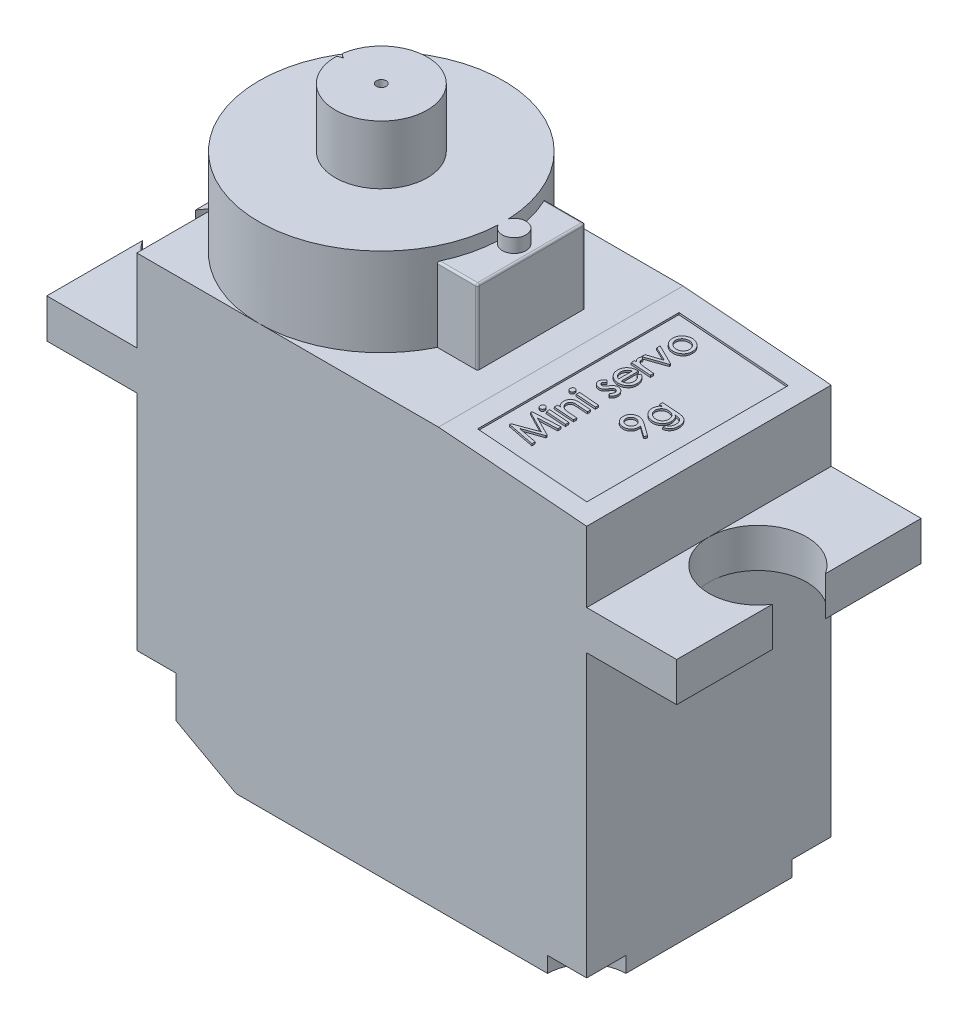
SolidWorks part; units mm, degrees
other "Camera1"
material "ABS"
ref_plane "Front Plane" through (0, 0, 0) normal (0, 0, 1) x (1, 0, 0)
ref_plane "Top Plane" through (0, 0, 0) normal (0, 1, 0) x (1, 0, 0)
ref_plane "Right Plane" through (0, 0, 0) normal (1, 0, 0) x (0, 0, -1)
sketch "Sketch1" plane through (0, 0, 0) normal (0, 1, 0) x (1, 0, 0)
  line L1 (11.5, -6.25) -> (-11.5, -6.25)
  line L2 (11.5, -6.25) -> (11.5, 6.25)
  line L3 (11.5, 6.25) -> (-11.5, 6.25)
  line L4 (-11.5, -6.25) -> (-11.5, 6.25)
  line L5 (11.5, -6.25) -> (-11.5, 6.25) construction
  line L6 (11.5, 6.25) -> (-11.5, -6.25) construction
  point P0 (0, 0)
  dimension "D1" = 12.5
  dimension "D2" = 23
extrude "Boss-Extrude1" add sketch "Sketch1" along normal blind 15.2
sketch "Sketch2" plane through (0, 15.2, 0) normal (0, 1, 0) x (1, 0, 0)
  line L1 (16.1, -6.25) -> (-16.1, -6.25)
  line L2 (16.1, -6.25) -> (16.1, 6.25)
  line L3 (16.1, 6.25) -> (-16.1, 6.25)
  line L4 (-16.1, -6.25) -> (-16.1, 6.25)
  line L5 (16.1, -6.25) -> (-16.1, 6.25) construction
  line L6 (16.1, 6.25) -> (-16.1, -6.25) construction
  point P0 (0, 0)
  dimension "D1" = 4.6
extrude "Boss-Extrude2" add sketch "Sketch2" along normal blind 2
sketch "Sketch3" plane through (0, 17.2, 0) normal (0, 1, 0) x (1, 0, 0)
  line L0 (16.1, 6.25) -> (-16.1, 6.25) construction
  line L1 (11.5, -6.25) -> (-11.5, -6.25)
  line L2 (11.5, -6.25) -> (11.5, 6.25)
  line L3 (11.5, 6.25) -> (-11.5, 6.25)
  line L4 (-11.5, -6.25) -> (-11.5, 6.25)
  line L5 (11.5, -6.25) -> (-11.5, 6.25) construction
  line L6 (11.5, 6.25) -> (-11.5, -6.25) construction
  point P0 (0, 0)
  dimension "D1" = 23
extrude "Boss-Extrude3" add sketch "Sketch3" along normal blind 4.2
sketch "Sketch4" plane through (0, 0, 6.25) normal (0, 0, 1) x (1, 0, 0)
  line L0 (11.5, 20.8) -> (3.9237, 21.4)
  line L1 (11.5, 21.4) -> (11.5, 17.2) construction
  line L2 (-11.5, 21.4) -> (11.5, 21.4) construction
  line L3 (3.9237, 21.4) -> (11.5, 21.4)
  line L4 (11.5, 21.4) -> (11.5, 20.8)
  dimension "D1" = 3.6
  dimension "D2" = 7.6
extrude "Cut-Extrude1" cut sketch "Sketch4" against normal through all
sketch "Sketch5" plane through (0, 21.4, 0) normal (0, 1, 0) x (1, 0, 0)
  line L0 (3.9237, 6.25) -> (-11.5, 6.25) construction
  line L2 (-11.5, 6.25) -> (-11.5, -6.25) construction
  line L3 (-11.5, -6.25) -> (3.9237, -6.25) construction
  circle A0 centre (-5.25, 0) radius 6.25
extrude "Boss-Extrude4" add sketch "Sketch5" along normal blind 4.5
sketch "Sketch6" plane through (0, 21.4, 0) normal (0, 1, 0) x (1, 0, 0)
  line L0 (3.9237, 6.25) -> (3.9237, -6.25) construction
  line L1 (-2.4237, -2.75) -> (2.4237, -2.75)
  line L2 (-2.4237, -2.75) -> (-2.4237, 2.75)
  line L3 (-2.4237, 2.75) -> (2.4237, 2.75)
  line L4 (2.4237, -2.75) -> (2.4237, 2.75)
  line L5 (-2.4237, -2.75) -> (2.4237, 2.75) construction
  line L6 (-2.4237, 2.75) -> (2.4237, -2.75) construction
  point P0 (0, 0)
  dimension "D1" = 1.5
  dimension "D2" = 5.5
extrude "Boss-Extrude5" add sketch "Sketch6" along normal blind 3.8
sketch "Sketch7" plane through (0, 25.2, 0) normal (0, 1, 0) x (1, 0, 0)
  circle A0 centre (1.5423, 0) radius 0.6059
extrude "Boss-Extrude7" add sketch "Sketch7" along normal up to surface (0.7 mm away) up to face at (-5.25, 25.9, 6.25)
sketch "Sketch8" plane through (0, 25.9, 0) normal (0, 1, 0) x (1, 0, 0)
  circle A0 centre (-5.25, 0) radius 2.35
  dimension "D1" = 4.7
extrude "Boss-Extrude8" add sketch "Sketch8" along normal blind 3
sketch "Sketch9" plane through (0, 0, 6.25) normal (0, 0, 1) x (1, 0, 0)
  line L0 (-11.5, 0) -> (-6.4206, 0)
  line L1 (-11.5, 0) -> (11.5, 0) construction
  line L2 (-6.4206, 0) -> (-11.5, 2.8)
  line L3 (-11.5, 15.2) -> (-11.5, 0) construction
  line L4 (-11.5, 2.8) -> (-11.5, 0)
  dimension "D1" = 5.8
  dimension "D2" = 2.8
extrude "Cut-Extrude2" cut sketch "Sketch9" against normal through all
sketch "Sketch12" plane through (0, 17.2, 0) normal (0, 1, 0) x (1, 0, 0)
  line L1 (11.5, -6.25) -> (11.5, 6.25) construction
  line L5 (16.1, -6.25) -> (16.1, 6.25) construction
  line L6 (16.1, 0) -> (14, 0) construction
  circle A0 centre (14, 0) radius 2.5
  dimension "D1" = 5
sketch "Sketch13" plane through (0, 28.9, 0) normal (0, 1, 0) x (1, 0, 0)
  circle A0 centre (-5.25, 0) radius 0.25
  dimension "D1" = 0.5
extrude "Cut-Extrude3" cut sketch "Sketch13" against normal up to surface (7.5 mm away) up to face at (-7.3333, 21.4, -5.2083)
sketch "Sketch14" plane through (0, 28.9, 0) normal (0, 1, 0) x (1, 0, 0)
  arc A2 (-7.5996, 0.0428) -> (-7.2948, 0.1462) centre (-7.3494, -0.1935) cw
  arc A4 (-7.2948, 0.1462) -> (-7.5727, 0.357) centre (-7.1646, 0.6066) cw
  arc A5 (-7.5727, 0.357) -> (-7.5996, 0.0428) centre (-6.4433, 0.1021) ccw
  circle M2 centre (-5.25, 0) radius 2.35
extrude "Cut-Extrude10" cut sketch "Sketch14" against normal up to surface (3 mm away) contours A2 A4 M2
extrude "Cut-Extrude11" cut sketch "Sketch12" against normal blind 10
mirror "Mirror1" about plane through (0, 0, 0) normal (1, 0, 0) of "Cut-Extrude11"
sketch "Sketch15" plane through (0, 0, 0) normal (0, -1, 0) x (1, 0, 0)
  line L0 (11.5, 6.25) -> (11.5, -6.25) construction
  line L1 (-6.4206, 6.25) -> (11.5, 6.25) construction
  line L2 (9.5, 6.25) -> (11.5, 6.25)
  line L3 (11.5, 6.25) -> (11.5, 4.25)
  line L4 (4.5258, 0) -> (-4.7559, 0) construction
  line L5 (11.5, -6.25) -> (11.5, -4.25)
  line L6 (9.5, -6.25) -> (11.5, -6.25)
  arc A0 (11.5, 4.25) -> (9.5, 6.25) centre (11.5, 6.25) cw
  arc A1 (11.5, -4.25) -> (9.5, -6.25) centre (11.5, -6.25) ccw
  dimension "D1" = 2
extrude "Cut-Extrude12" cut sketch "Sketch15" against normal blind 0.8
sketch "Sketch16" plane through (0, 0, 0) normal (0, -1, 0) x (1, 0, 0)
  line L0 (-6.4206, 6.25) -> (-11.5, 6.25) construction
  line L1 (-11.5, -6.25) -> (-11.5, 6.25) construction
  line L2 (-11.5, 0) -> (-11.5, 6.25) construction
  line L3 (-11.5, 4.25) -> (-11.5, 6.25)
  line L4 (-11.5, 6.25) -> (-9.5, 6.25)
  line L5 (-1.3995, 0) -> (2.6342, 0) construction
  line L6 (-11.5, -6.25) -> (-9.5, -6.25)
  line L7 (-11.5, -4.25) -> (-11.5, -6.25)
  arc A0 (-9.5, 6.25) -> (-11.5, 4.25) centre (-11.5, 6.25) cw
  arc A1 (-9.5, -6.25) -> (-11.5, -4.25) centre (-11.5, -6.25) ccw
  dimension "D1" = 2
extrude "Cut-Extrude13" cut sketch "Sketch16" against normal blind 3.8
sketch "Sketch17" plane through (1.7087, 21.5754, 0) normal (0.0789, 0.9969, 0) x (0.9969, -0.0789, 0)
  line L1 (8.822, -5.25) -> (3.222, -5.25)
  line L2 (8.822, -5.25) -> (8.822, 5.05)
  line L3 (8.822, 5.05) -> (3.222, 5.05)
  line L4 (3.222, -5.25) -> (3.222, 5.05)
  line L8 (2.222, 6.25) -> (2.222, -6.25) construction
  line L9 (9.822, 6.25) -> (9.822, -6.25) construction
  line L10 (2.222, -6.25) -> (9.822, -6.25) construction
  dimension "D1" = 1
  dimension "D2" = 1
  dimension "D3" = 1
  dimension "D4" = 10.3
extrude "Cut-Extrude14" cut sketch "Sketch17" against normal blind 0.1
sketch "Sketch19" plane through (1.7008, 21.4757, 0) normal (0.0789, 0.9969, 0) x (0.9969, -0.0789, 0)
  line L0 (5.1279, -5.25) -> (5.1279, 5.05) construction
  line L4 (3.222, -5.25) -> (8.822, -5.25) construction
  line L5 (8.822, 5.05) -> (3.222, 5.05) construction
  line L6 (7.5214, 5.05) -> (7.5214, -5.25) construction
  text T0 "<b>Mini servo</b>" font "Century Gothic" height in points 5
  text T1 "<b>9g</b>" font "Century Gothic" height in points 5
extrude "Boss-Extrude9" add sketch "Sketch19" along normal up to surface (0.1 mm away) up to face at (7.7119, 21.1, 0.1)
fillet "Fillet3" radius 0.1 5 edges at (2.4237, 25.2, 0) (1.3931, 25.2, 2.75) (2.4237, 23.3, 2.75) (2.4237, 23.3, -2.75) (1.3931, 25.2, -2.75)
